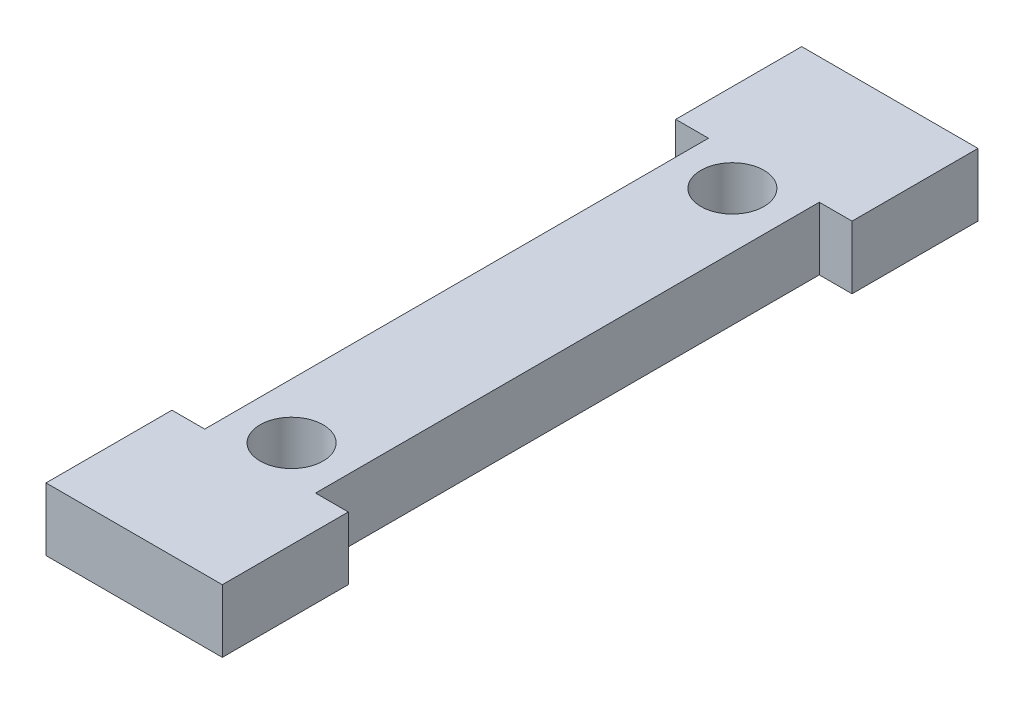
SolidWorks part; units mm, degrees
ref_plane "Front Plane" through (0, 0, 0) normal (0, 0, 1) x (1, 0, 0)
ref_plane "Top Plane" through (0, 0, 0) normal (0, 1, 0) x (1, 0, 0)
ref_plane "Right Plane" through (0, 0, 0) normal (1, 0, 0) x (0, 0, -1)
sketch "Sketch1" plane through (0, 0, 0) normal (0, 1, 0) x (1, 0, 0)
  line L0 (-3.302, 0) -> (14.478, 0)
  line L1 (14.478, 0) -> (14.478, 12.7)
  line L2 (14.478, 12.7) -> (11.176, 12.7)
  line L3 (11.176, 12.7) -> (11.176, 63.5)
  line L4 (11.176, 63.5) -> (14.478, 63.5)
  line L5 (14.478, 63.5) -> (14.478, 76.2)
  line L6 (14.478, 76.2) -> (-3.302, 76.2)
  line L7 (-3.302, 76.2) -> (-3.302, 63.5)
  line L8 (-3.302, 63.5) -> (0, 63.5)
  line L9 (0, 63.5) -> (0, 12.7)
  line L10 (0, 12.7) -> (-3.302, 12.7)
  line L11 (-3.302, 12.7) -> (-3.302, 0)
  line L12 (5.588, 76.2) -> (5.588, 0) construction
  circle A0 centre (5.588, 60.325) radius 3.175
  circle A1 centre (5.588, 15.875) radius 3.175
  point P20 (5.588, 38.1)
  dimension "D6" = 6.35
  dimension "D7" = 6.35
  dimension "D1" = 44.45
  dimension "D2" = 17.78
  dimension "D3" = 76.2
  dimension "D4" = 12.7
  dimension "D5" = 3.302
  dimension "D8" = 22.225
extrude "Boss-Extrude2" add sketch "Sketch1" along normal blind 6.35
